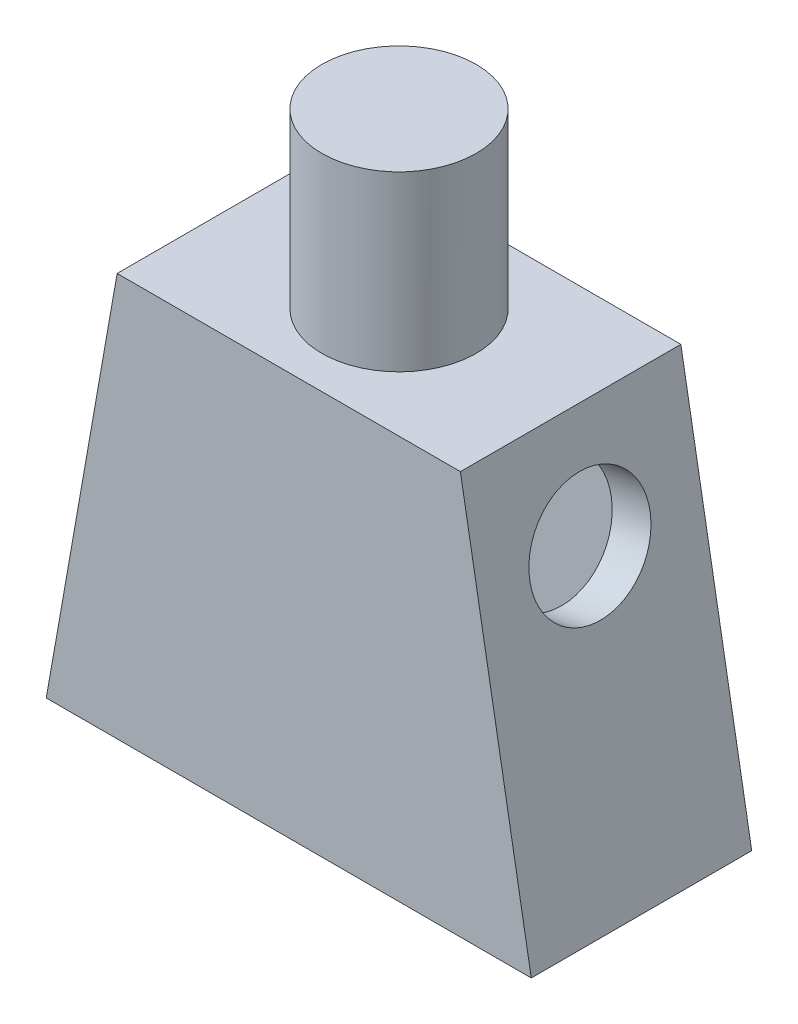
SolidWorks part; units mm, degrees
ref_plane "Front Plane" through (0, 0, 0) normal (0, 0, 1) x (1, 0, 0)
ref_plane "Top Plane" through (0, 0, 0) normal (0, 1, 0) x (1, 0, 0)
ref_plane "Right Plane" through (0, 0, 0) normal (1, 0, 0) x (0, 0, -1)
sketch "Sketch1" plane through (0, 0, 0) normal (0, 0, 1) x (1, 0, 0)
  line L0 (-5.45, 6.4) -> (-7.7, -6.4)
  line L1 (-7.7, 6.4) -> (7.7, 6.4) construction
  line L2 (-7.7, 6.4) -> (-7.7, -6.4) construction
  line L3 (-7.7, -6.4) -> (7.7, -6.4) construction
  line L4 (7.7, 6.4) -> (7.7, -6.4) construction
  line L5 (-7.7, 6.4) -> (7.7, -6.4) construction
  line L6 (-7.7, -6.4) -> (7.7, 6.4) construction
  line L7 (-5.45, 6.4) -> (5.45, 6.4) construction
  line L8 (-5.45, 6.4) -> (-5.45, -6.4) construction
  line L9 (-5.45, -6.4) -> (5.45, -6.4) construction
  line L10 (5.45, 6.4) -> (5.45, -6.4) construction
  line L11 (-5.45, 6.4) -> (5.45, -6.4) construction
  line L12 (-5.45, -6.4) -> (5.45, 6.4) construction
  line L13 (-7.7, -6.4) -> (7.7, -6.4)
  line L14 (7.7, -6.4) -> (5.45, 6.4)
  line L15 (5.45, 6.4) -> (-5.45, 6.4)
  point P0 (0, 0)
  point P6 (0, 0)
  dimension "D1" = 15.4
  dimension "D2" = 12.8
  dimension "D3" = 10.9
extrude "Extrude1" add sketch "Sketch1" along normal blind 7
shell "Shell1" thickness 1.25
sketch "Sketch2" plane through (0, 6.4, 0) normal (0, 1, 0) x (1, 0, 0)
  line L0 (5.45, 0) -> (-5.45, 0) construction
  line L1 (-5.45, -7) -> (-5.45, 0) construction
  circle A0 centre (0, -3.5) radius 2.45
  point P4 (0, 0)
  point P7 (-5.45, -3.5)
  dimension "D1" = 4.9
extrude "Extrude2" add sketch "Sketch2" along normal blind 5.5
sketch "Sketch3" plane through (-6.3779, 1.1211, 0) normal (-0.9849, 0.1731, 0) x (0, 0, 1)
  line L0 (7, 5.3598) -> (0, 5.3598) construction
  circle A0 centre (3.5, 1.8198) radius 1.91
  point P4 (3.5, 5.3598)
  dimension "D1" = 3.82
  dimension "D2" = 3.54
extrude "Extrude3" cut sketch "Sketch3" against normal up to next
sketch "Sketch4" plane through (6.3779, 1.1211, 0) normal (0.9849, 0.1731, 0) x (0, 0, -1)
  line L0 (-7, 5.3598) -> (0, 5.3598) construction
  circle A0 centre (-3.5, 1.8198) radius 1.91
  point P4 (-3.5, 5.3598)
  dimension "D1" = 3.82
  dimension "D2" = 3.54
extrude "Extrude4" cut sketch "Sketch4" against normal up to next
